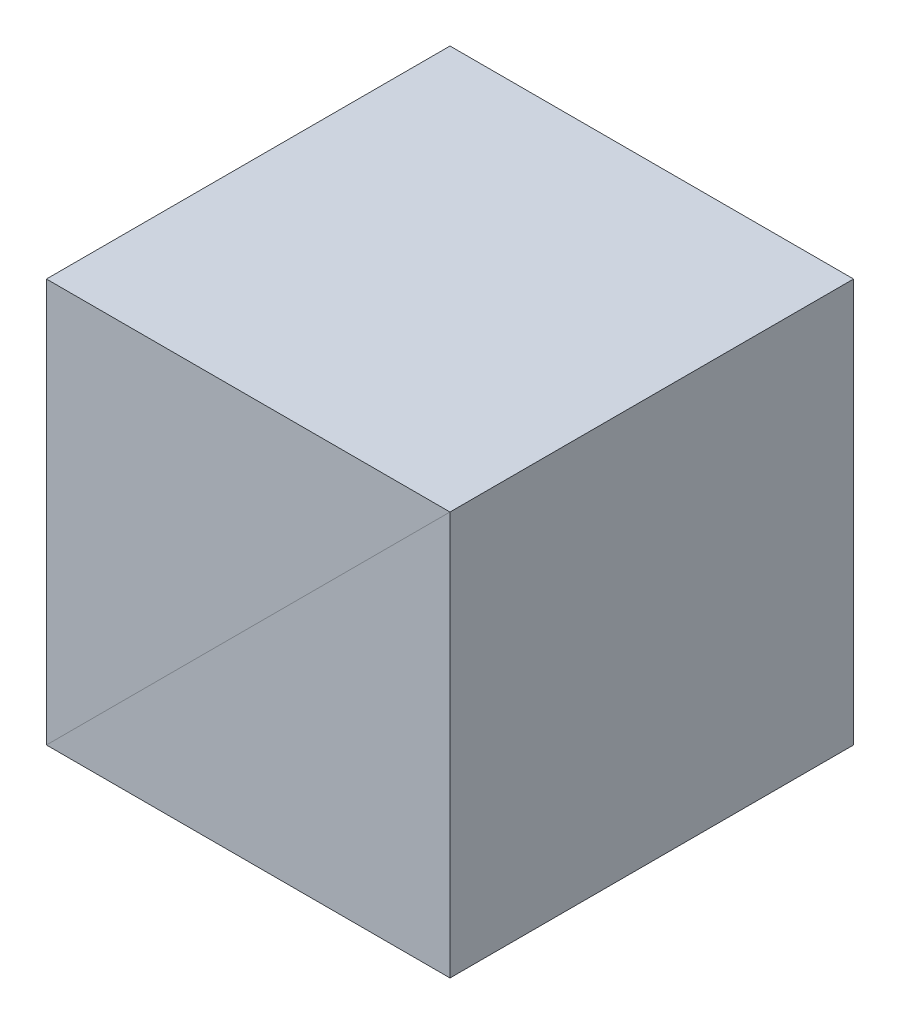
SolidWorks part; units mm, degrees
ref_plane "前视基准面" through (0, 0, 0) normal (0, 0, 1) x (1, 0, 0)
ref_plane "上视基准面" through (0, 0, 0) normal (0, 1, 0) x (1, 0, 0)
ref_plane "右视基准面" through (0, 0, 0) normal (1, 0, 0) x (0, 0, -1)
sketch "草图1" plane through (0, 0, 0) normal (0, 0, 1) x (1, 0, 0)
  line L3 (-7.5, -7.5) -> (7.5, -7.5)
  line L4 (7.5, 7.5) -> (7.5, -7.5)
  line L5 (7.5, 7.5) -> (-7.5, -7.5)
  dimension "D1" = 15
extrude "凸台-拉伸1" add sketch "草图1" along normal mid plane 15
mirror "镜向2" about plane through (7.5, 7.5, 7.5) normal (0.7071, -0.7071, 0) of bodies 107
